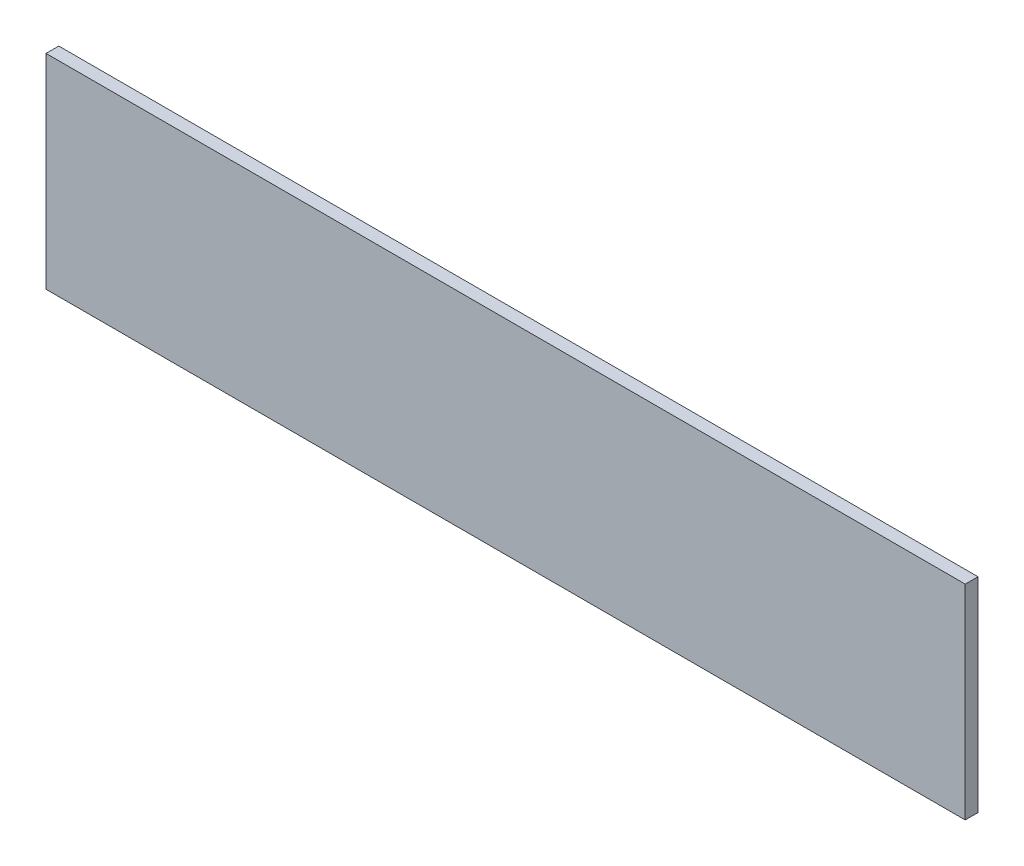
SolidWorks part; units mm, degrees
material "Nylon 6/10"
ref_plane "Front Plane" through (0, 0, 0) normal (0, 0, 1) x (1, 0, 0)
ref_plane "Top Plane" through (0, 0, 0) normal (0, 1, 0) x (1, 0, 0)
ref_plane "Right Plane" through (0, 0, 0) normal (1, 0, 0) x (0, 0, -1)
sketch "Sketch1" plane through (0, 0, 0) normal (0, 0, 1) x (1, 0, 0)
  line L6 (0, 0) -> (-228.6, 0)
  line L7 (0, 0) -> (0, -50.8)
  line L8 (0, -50.8) -> (-228.6, -50.8)
  line L9 (-228.6, 0) -> (-228.6, -50.8)
  dimension "D1" = 50.8
  dimension "D2" = 228.6
extrude "Boss-Extrude1" add sketch "Sketch1" along normal blind 3.175
ref_plane "Plane1" through (0, -25.4, 0) normal (0, 1, 0) x (1, 0, 0)
